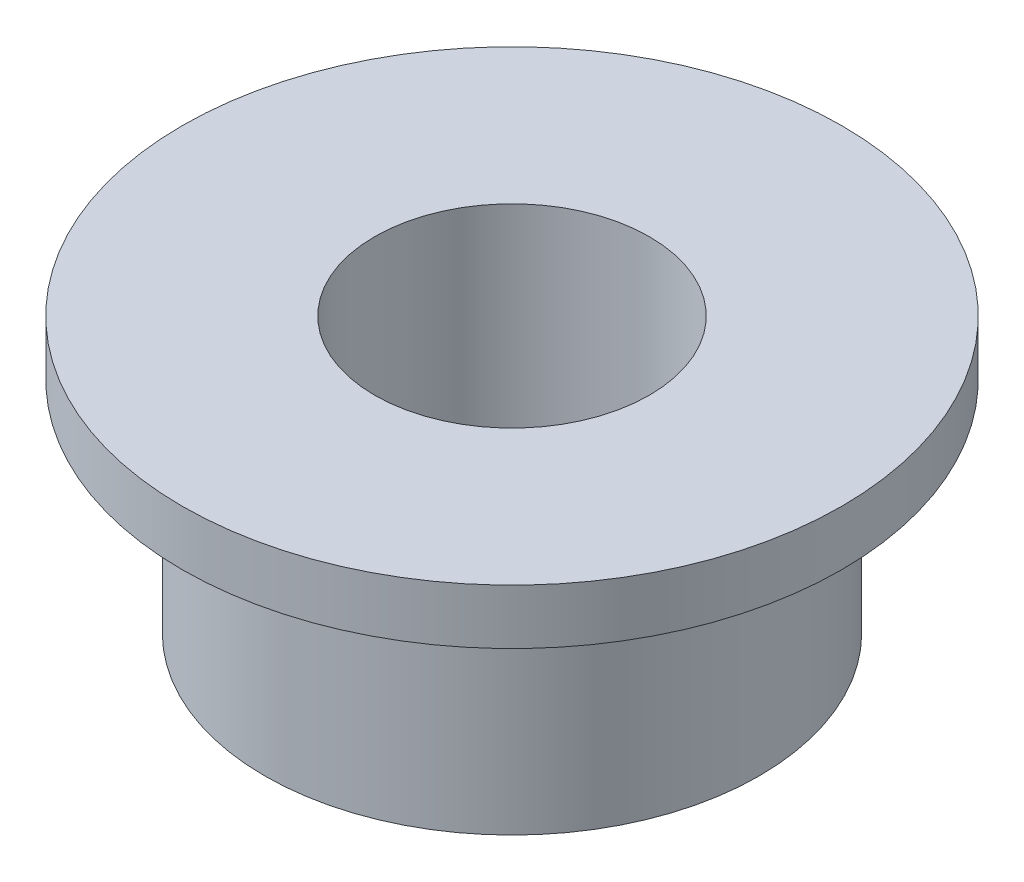
SolidWorks part; units mm, degrees
ref_plane "Front Plane" through (0, 0, 0) normal (0, 0, 1) x (1, 0, 0)
ref_plane "Top Plane" through (0, 0, 0) normal (0, 1, 0) x (1, 0, 0)
ref_plane "Right Plane" through (0, 0, 0) normal (1, 0, 0) x (0, 0, -1)
sketch "Sketch1" plane through (0, 0, 0) normal (0, 0, 1) x (1, 0, 0)
  line L0 (0, 0) -> (15, 0)
  line L1 (15, 0) -> (15, 10)
  line L2 (15, 10) -> (-20, 10)
  line L3 (-20, 10) -> (-20, -40)
  line L4 (-20, -40) -> (0, -40)
  line L5 (0, -40) -> (0, 0)
  line L6 (-45, -15) -> (-45, -40) construction
  dimension "D1" = 35
  dimension "D2" = 50
  dimension "D3" = 40
  dimension "D4" = 20
  dimension "D5" = 25
revolve "Revolve1" add sketch "Sketch1" angle 360 about L6
